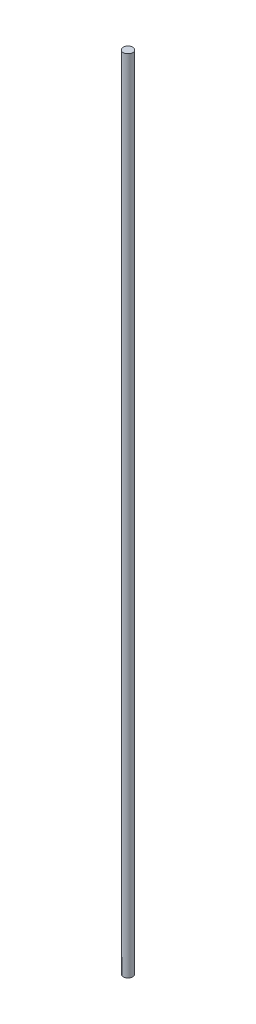
SolidWorks part; units mm, degrees
material "Liga 1060"
ref_plane "Plano frontal" through (0, 0, 0) normal (0, 0, 1) x (1, 0, 0)
ref_plane "Plano superior" through (0, 0, 0) normal (0, 1, 0) x (1, 0, 0)
ref_plane "Plano direito" through (0, 0, 0) normal (1, 0, 0) x (0, 0, -1)
sketch "Esboço1" plane through (0, 0, 0) normal (0, 1, 0) x (1, 0, 0)
  circle A0 centre (0, 0) radius 3.97
  dimension "D1" = 7.94
extrude "Ressalto-extrusão1" add sketch "Esboço1" along normal mid plane 670
